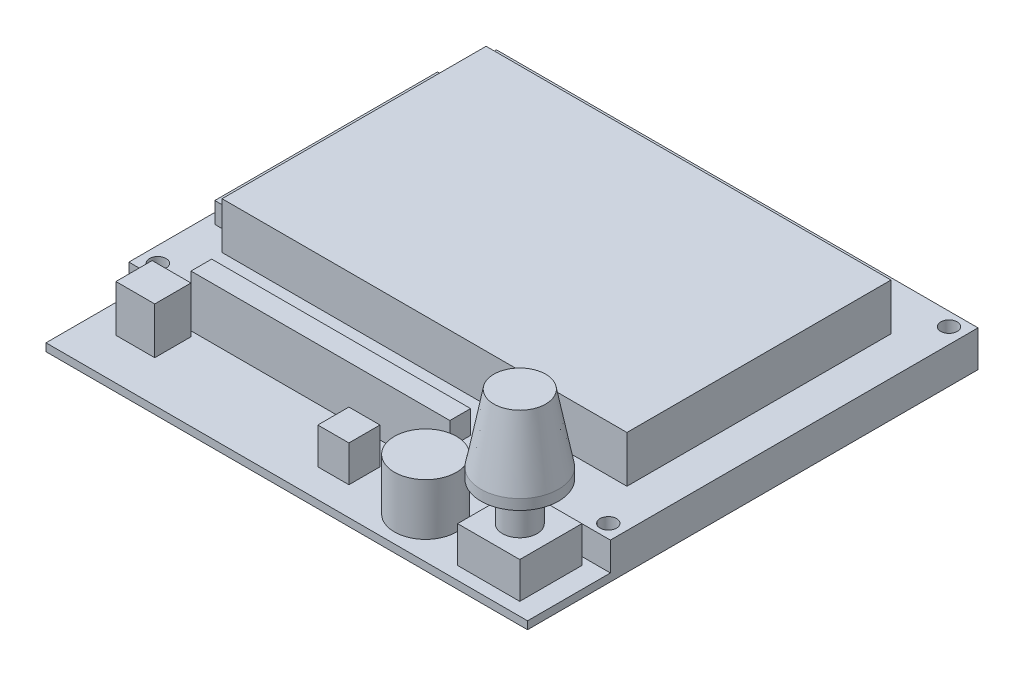
SolidWorks part; units mm, degrees
ref_plane "Спереди" through (0, 0, 0) normal (0, 0, 1) x (1, 0, 0)
ref_plane "Сверху" through (0, 0, 0) normal (0, 1, 0) x (1, 0, 0)
ref_plane "Справа" through (0, 0, 0) normal (1, 0, 0) x (0, 0, -1)
sketch "Эскиз1" plane through (0, 0, 0) normal (0, 1, 0) x (1, 0, 0)
  line L0 (0, 0) -> (93, 0)
  line L1 (0, 0) -> (0, 87)
  line L2 (93, 0) -> (93, 87)
  line L3 (0, 87) -> (93, 87)
  line L4 (3, 84.4) -> (90, 84.4) construction
  line L5 (3, 84.4) -> (3, 18.6) construction
  line L6 (90, 84.4) -> (90, 18.6) construction
  line L7 (3, 18.6) -> (90, 18.6) construction
  line L8 (46.5, 84.4) -> (46.5, 18.6) construction
  line L10 (46.5, 87) -> (46.5, 0) construction
  line L11 (93, 43.5) -> (0, 43.5) construction
  circle A0 centre (3, 84.4) radius 1.6
  circle A1 centre (90, 84.4) radius 1.6
  circle A2 centre (90, 18.6) radius 1.6
  circle A3 centre (3, 18.6) radius 1.6
  dimension "D6" = 3.2
  dimension "D7" = 3.2
  dimension "D8" = 3.2
  dimension "D9" = 3.2
  dimension "D1" = 93
  dimension "D2" = 87
  dimension "D3" = 87
  dimension "D4" = 65.8
  dimension "D5" = 2.6
extrude "Бобышка-Вытянуть1" add sketch "Эскиз1" along normal blind 7
sketch "Эскиз2" plane through (0, 0, 0) normal (0, -1, 0) x (1, 0, 0)
  line L0 (46.5, -87) -> (46.5, 0) construction
  line L1 (93, -87) -> (0, -87) construction
  line L2 (0, 0) -> (93, 0) construction
  line L3 (0, -43.5) -> (93, -43.5) construction
  line L4 (0, -87) -> (0, 0) construction
  line L5 (93, 0) -> (93, -87) construction
sketch "Эскиз3" plane through (0, 7, 0) normal (0, 1, 0) x (1, 0, 0)
  line L0 (0, 0) -> (93, 0)
  line L1 (0, 0) -> (0, 16)
  line L2 (93, 0) -> (93, 16)
  line L3 (0, 16) -> (93, 16)
  line L4 (93, 87) -> (0, 87) construction
  dimension "D1" = 71
extrude "Вырез-Вытянуть1" cut sketch "Эскиз3" against normal blind 5.5
sketch "Эскиз4" plane through (0, 7, 0) normal (0, 1, 0) x (1, 0, 0)
  line L0 (7.4, 77.6) -> (85.6, 77.6)
  line L1 (7.4, 77.6) -> (7.4, 26.6)
  line L2 (85.6, 77.6) -> (85.6, 26.6)
  line L3 (7.4, 26.6) -> (85.6, 26.6)
  line L4 (93, 87) -> (0, 87) construction
  line L5 (0, 87) -> (0, 16) construction
  line L6 (93, 16) -> (93, 87) construction
  dimension "D1" = 9.4
  dimension "D2" = 7.4
  dimension "D3" = 78.2
  dimension "D4" = 51
  dimension "D5" = 7.4
extrude "Бобышка-Вытянуть2" add sketch "Эскиз4" along normal blind 9
sketch "Эскиз5" plane through (0, 1.5, 0) normal (0, 1, 0) x (1, 0, 0)
  line L0 (77, 14.5) -> (89, 14.5)
  line L1 (77, 14.5) -> (77, 2.5)
  line L2 (89, 14.5) -> (89, 2.5)
  line L3 (77, 2.5) -> (89, 2.5)
  line L4 (93, 0) -> (93, 16) construction
  line L5 (0, 0) -> (93, 0) construction
  dimension "D1" = 4
  dimension "D2" = 2.5
  dimension "D3" = 12
  dimension "D4" = 12
extrude "Бобышка-Вытянуть3" add sketch "Эскиз5" along normal blind 7
sketch "Эскиз6" plane through (0, 8.5, 0) normal (0, 1, 0) x (1, 0, 0)
  line L0 (83, 14.5) -> (83, 2.5) construction
  line L1 (89, 14.5) -> (77, 14.5) construction
  line L2 (77, 2.5) -> (89, 2.5) construction
  circle A0 centre (83, 8.5) radius 3.35
  dimension "D1" = 6.7
extrude "Бобышка-Вытянуть4" add sketch "Эскиз6" along normal blind 7.5
sketch "Эскиз8" plane through (0, 16, 0) normal (0, 1, 0) x (1, 0, 0)
  line L0 (83, 11.85) -> (83, 5.15) construction
  circle A0 centre (83, 8.5) radius 3.35 construction
ref_plane "Плоскость1" through (83, 0, 0) normal (-1, 0, 0) x (0, 0, 1)
sketch "Эскиз9" plane through (83, 0, 0) normal (-1, 0, 0) x (0, 0, 1)
  line L0 (-8.5, 16) -> (-16, 16)
  line L1 (-11.85, 16) -> (-5.15, 16) construction
  line L2 (-16, 16) -> (-16, 18)
  line L3 (-16, 18) -> (-13.5, 31)
  line L4 (-13.5, 31) -> (-8.5, 31)
  line L6 (-5.15, 16) -> (-11.85, 16) construction
  line L7 (-5.15, 16) -> (-11.85, 16) construction
  line L8 (-8.5, 16) -> (-8.5, 31) construction
  line L9 (-8.5, 16) -> (-8.5, 31)
  dimension "D1" = 15
  dimension "D2" = 2
  dimension "D3" = 5
  dimension "D4" = 7.5
sketch "Sketch1" plane through (0, 7, 0) normal (0, 1, 0) x (1, 0, 0)
  line L0 (7.4, 73.6) -> (7.4, 30.6)
  line L1 (7.4, 73.6) -> (2, 73.6)
  line L2 (7.4, 30.6) -> (2, 30.6)
  line L3 (2, 73.6) -> (2, 30.6)
  line L4 (7.4, 77.6) -> (7.4, 26.6) construction
  line L5 (0, 87) -> (0, 16) construction
  line L6 (85.6, 77.6) -> (7.4, 77.6) construction
  line L7 (7.4, 26.6) -> (85.6, 26.6) construction
  dimension "D1" = 2
  dimension "D2" = 4
  dimension "D3" = 4
extrude "Boss-Extrude1" add sketch "Sketch1" along normal blind 4
revolve "Revolve1" add sketch "Эскиз9" angle 360 about L9
sketch "Sketch2" plane through (0, 1.5, 0) normal (0, 1, 0) x (1, 0, 0)
  line L0 (93, 0) -> (93, 16) construction
  line L1 (0, 0) -> (93, 0) construction
  circle A0 centre (65.3, 8) radius 6
  dimension "D1" = 12
  dimension "D3" = 8
  dimension "D2" = 27.7
extrude "Boss-Extrude2" add sketch "Sketch2" along normal blind 10
sketch "Sketch3" plane through (0, 7, 0) normal (0, 1, 0) x (1, 0, 0)
  line L0 (12, 16) -> (62, 16)
  line L1 (12, 16) -> (12, 20)
  line L2 (62, 16) -> (62, 20)
  line L3 (12, 20) -> (62, 20)
  line L4 (93, 16) -> (0, 16) construction
  line L5 (0, 87) -> (0, 16) construction
  dimension "D1" = 12
  dimension "D2" = 50
  dimension "D3" = 4
extrude "Boss-Extrude3" add sketch "Sketch3" along normal blind 4.5
sketch "Sketch4" plane through (0, 1.5, 0) normal (0, 1, 0) x (1, 0, 0)
  line L0 (5.5, 15) -> (13, 15)
  line L1 (5.5, 15) -> (5.5, 8)
  line L2 (13, 15) -> (13, 8)
  line L3 (5.5, 8) -> (13, 8)
  line L4 (0, 0) -> (93, 0) construction
  line L5 (0, 16) -> (0, 0) construction
  dimension "D1" = 15
  dimension "D2" = 13
  dimension "D3" = 7.5
  dimension "D4" = 7
extrude "Boss-Extrude4" add sketch "Sketch4" along normal blind 9
sketch "Sketch5" plane through (0, 1.5, 0) normal (0, 1, 0) x (1, 0, 0)
  line L0 (47, 11.5) -> (53, 11.5)
  line L1 (47, 11.5) -> (47, 5.5)
  line L2 (53, 11.5) -> (53, 5.5)
  line L3 (47, 5.5) -> (53, 5.5)
  line L4 (93, 0) -> (93, 16) construction
  line L5 (0, 0) -> (93, 0) construction
  dimension "D1" = 46
  dimension "D2" = 11.5
  dimension "D3" = 6
  dimension "D4" = 6
extrude "Boss-Extrude5" add sketch "Sketch5" along normal blind 7
